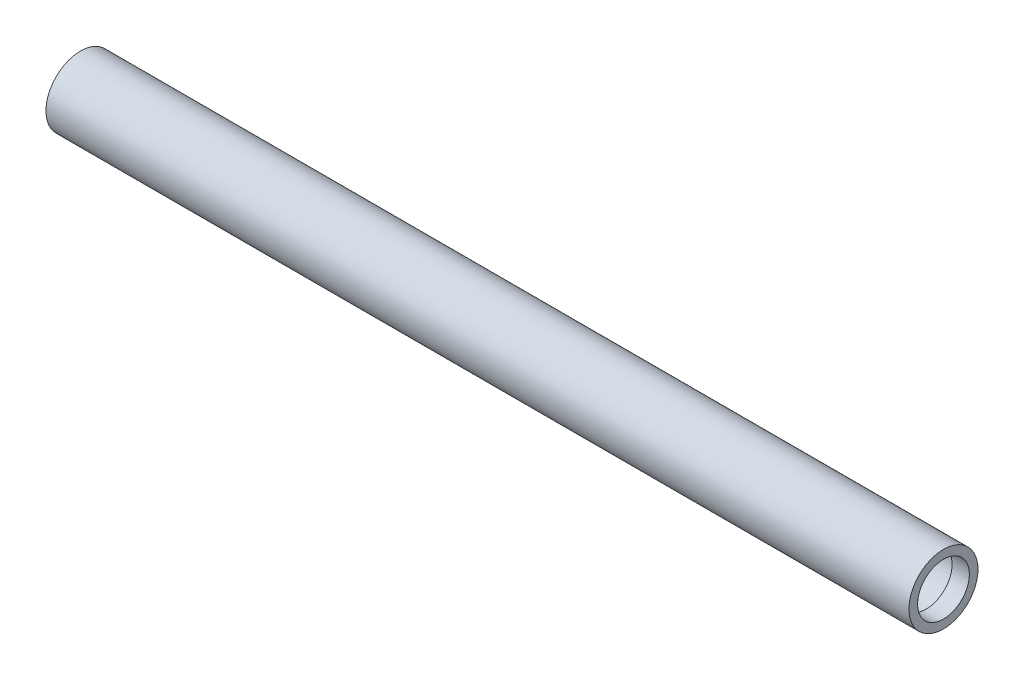
SolidWorks part; units mm, degrees
ref_plane "Front Plane" through (0, 0, 0) normal (0, 0, 1) x (1, 0, 0)
ref_plane "Top Plane" through (0, 0, 0) normal (0, 1, 0) x (1, 0, 0)
ref_plane "Right Plane" through (0, 0, 0) normal (1, 0, 0) x (0, 0, -1)
sketch "Sketch1" plane through (0, 0, 0) normal (1, 0, 0) x (0, 0, -1)
  circle A0 centre (0, 0) radius 18
  circle A1 centre (0, 0) radius 20
extrude "Boss-Extrude1" add sketch "Sketch1" along normal blind 500
sketch "Sketch2" plane through (0, 0, 0) normal (-1, 0, 0) x (0, 0, 1)
  circle A0 centre (0, 0) radius 10
  circle A1 centre (0, 0) radius 18
extrude "Boss-Extrude2" add sketch "Sketch2" against normal blind 10
sketch "Sketch5" plane through (500, 0, 0) normal (1, 0, 0) x (0, 0, -1)
  circle A0 centre (0, 0) radius 15
  circle A2 centre (0, 0) radius 18
extrude "Boss-Extrude3" add sketch "Sketch5" against normal blind 10
